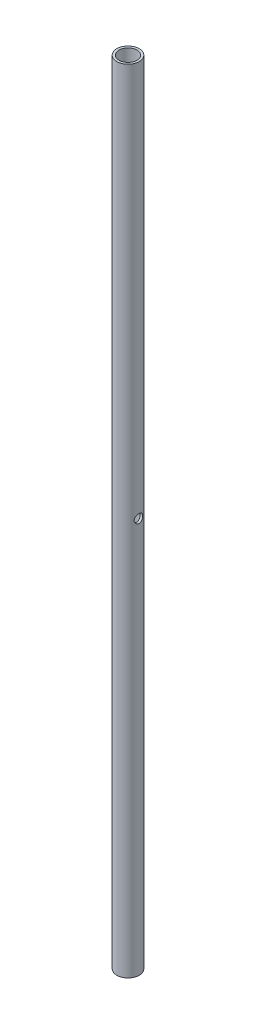
SolidWorks part; units mm, degrees
material "6061-T6 (SS)"
ref_plane "Front Plane" through (0, 0, 0) normal (0, 0, 1) x (1, 0, 0)
ref_plane "Top Plane" through (0, 0, 0) normal (0, 1, 0) x (1, 0, 0)
ref_plane "Right Plane" through (0, 0, 0) normal (1, 0, 0) x (0, 0, -1)
sketch "Sketch1" plane through (0, 0, 0) normal (0, 1, 0) x (1, 0, 0)
  circle A0 centre (0, 0) radius 16.7005
  circle A1 centre (0, 0) radius 13.335
  dimension "D1" = 33.401
  dimension "D2" = 26.67
extrude "Boss-Extrude1" add sketch "Sketch1" along normal blind 520.7
sketch "Sketch3" plane through (0, 0, 0) normal (0, -1, 0) x (1, 0, 0)
  circle A0 centre (0, 0) radius 13.335 construction
  circle A1 centre (0, 0) radius 16.7005
  circle A2 centre (0, 0) radius 16.7005
  circle A3 centre (0, 0) radius 13.335
  dimension "D1" = 0
extrude "Boss-Extrude2" add sketch "Sketch3" along normal blind 660.4
sketch "Sketch2" plane through (0, 0, 0) normal (1, 0, 0) x (0, 0, -1)
  line L1 (0, 18.3705) -> (0, -18.3705) construction
  line L2 (0, 520.7) -> (0, -660.4) construction
  line L3 (13.335, 520.7) -> (-13.335, 520.7) construction
  line L4 (-16.7005, -660.4) -> (16.7005, -660.4) construction
  circle A0 centre (0, -69.85) radius 6.35
  dimension "D1" = 12.7
extrude "Cut-Extrude1" cut sketch "Sketch2" against normal through all both and the other way through all
